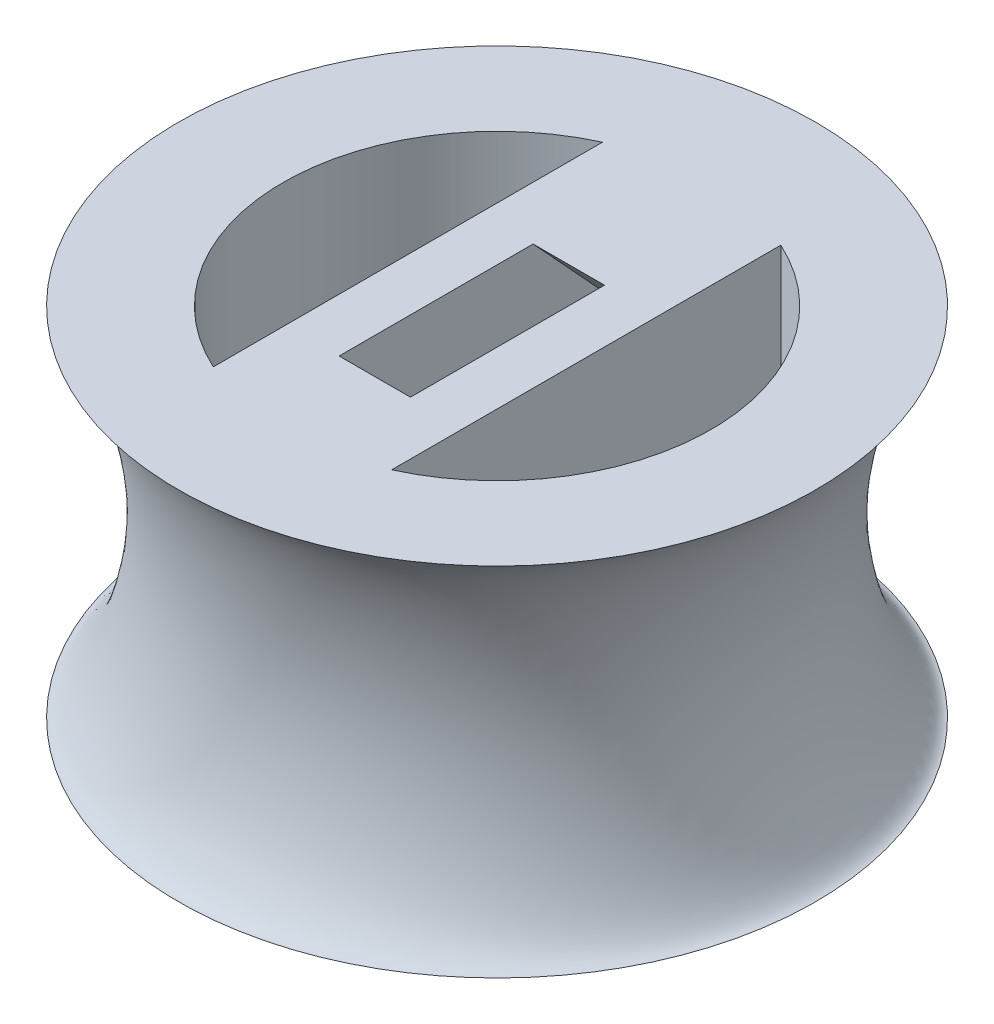
SolidWorks part; units mm, degrees
ref_plane "Front Plane" through (0, 0, 0) normal (0, 0, 1) x (1, 0, 0)
ref_plane "Top Plane" through (0, 0, 0) normal (0, 1, 0) x (1, 0, 0)
ref_plane "Right Plane" through (0, 0, 0) normal (1, 0, 0) x (0, 0, -1)
sketch "Sketch2" plane through (0, 0, 0) normal (0, 1, 0) x (1, 0, 0)
  circle A0 centre (0, 0) radius 9
  dimension "D1" = 18
extrude "Boss-Extrude1" add sketch "Sketch2" along normal blind 10
sketch "Sketch3" plane through (0, 0, 0) normal (0, 0, 1) x (1, 0, 0)
  line L0 (0, 0) -> (0, 10)
  line L1 (9, 10) -> (-9, 10) construction
  line L2 (-9, 0) -> (-9, 10)
  spline S0 degree 3 poles (-10.2536, -4.9188) (-10.2536, 14.9188) (-6.3208, 5) (-10.2536, -4.9188) (-10.2536, 14.9188) (-6.3208, 5) knots -1 -0.743391 -0.486783 0 0.256609 0.513217 1 1.256609 1.513217 2 only from (-9, 10) to (-9, 10)
  dimension "D1" = 1.67
revolve "Cut-Revolve1" cut sketch "Sketch3" angle 360 about L0
sketch "Sketch4" plane through (0, 10, 0) normal (0, 1, 0) x (1, 0, 0)
  line L0 (0, -6) -> (0, 6)
  line L1 (-6, 0) -> (6, 0)
  line L2 (2.5, -5.4544) -> (2.5, 5.4544)
  line L3 (-2.5, -5.4544) -> (-2.5, 5.4544)
  circle A0 centre (0, 0) radius 6
  point P5 (0, 0)
  point P9 (0, 0)
  point P12 (2.5, 0)
  point P15 (-2.5, 0)
  dimension "D1" = 12
  dimension "D2" = 5
extrude "Cut-Extrude1" cut sketch "Sketch4" against normal through all contours L3 A0 L1 | L1 A0 L3 | L2 A0 L1 | L1 A0 L2
ref_plane "Plane1" through (0, 0, 0) normal (-1, 0, 0) x (0, 0, 1)
sketch "Sketch5" plane through (0, 0, 0) normal (-1, 0, 0) x (0, 0, 1)
  line L0 (-2.0111, 10) -> (-4.5202, 7.2766)
  line L1 (5.4544, 10) -> (-5.4544, 10) construction
  line L2 (-4.4623, 5.8636) -> (-2.9914, 4.5084)
  line L3 (-1.5783, 4.5663) -> (3.4276, 10)
  line L4 (3.4276, 10) -> (-2.0111, 10)
  arc A0 (-2.9914, 4.5084) -> (-1.5783, 4.5663) centre (-2.3138, 5.2439) ccw
  arc A1 (-4.4623, 5.8636) -> (-4.5202, 7.2766) centre (-3.7847, 6.599) cw
  dimension "D2" = 1
  dimension "D3" = 1
  dimension "D1" = 4
extrude "Cut-Extrude2" cut sketch "Sketch5" against normal blind 1 and the other way blind 1
